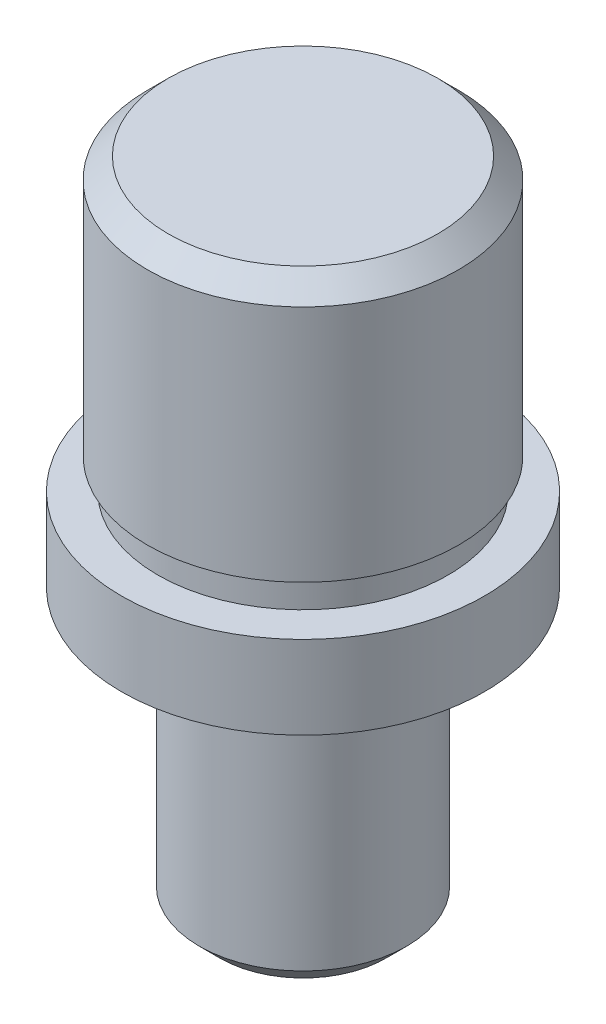
SolidWorks part; units mm, degrees
ref_plane "前视基准面" through (0, 0, 0) normal (0, 0, 1) x (1, 0, 0)
ref_plane "上视基准面" through (0, 0, 0) normal (0, 1, 0) x (1, 0, 0)
ref_plane "右视基准面" through (0, 0, 0) normal (1, 0, 0) x (0, 0, -1)
sketch "草图1" plane through (0, 0, 0) normal (0, 1, 0) x (1, 0, 0)
  circle A0 centre (0, 0) radius 17.5
  dimension "D1" = 35
extrude "凸台-拉伸1" add sketch "草图1" along normal blind 63
sketch "草图2" plane through (0, 63, 0) normal (0, 1, 0) x (1, 0, 0)
  circle A0 centre (0, 0) radius 15
  dimension "D1" = 30
extrude "切除-拉伸1" cut sketch "草图2" against normal blind 25 flip side to cut
sketch "草图3" plane through (0, 38, 0) normal (0, 1, 0) x (1, 0, 0)
  circle A0 centre (0, 0) radius 14
  dimension "D1" = 28
extrude "切除-拉伸2" cut sketch "草图3" against normal blind 3 flip side to cut
sketch "草图4" plane through (0, 0, 0) normal (0, -1, 0) x (1, 0, 0)
  circle A0 centre (0, 0) radius 10
  dimension "D1" = 20
extrude "切除-拉伸3" cut sketch "草图4" against normal blind 25 flip side to cut
sketch "草图5" plane through (0, 25, 0) normal (0, -1, 0) x (1, 0, 0)
  circle A0 centre (0, 0) radius 9
  dimension "D1" = 18
extrude "切除-拉伸4" cut sketch "草图5" against normal blind 2 flip side to cut
chamfer "倒角1" distance 2 angle 45 2 edges at (0, 63, 15) (0, 0, -10)
